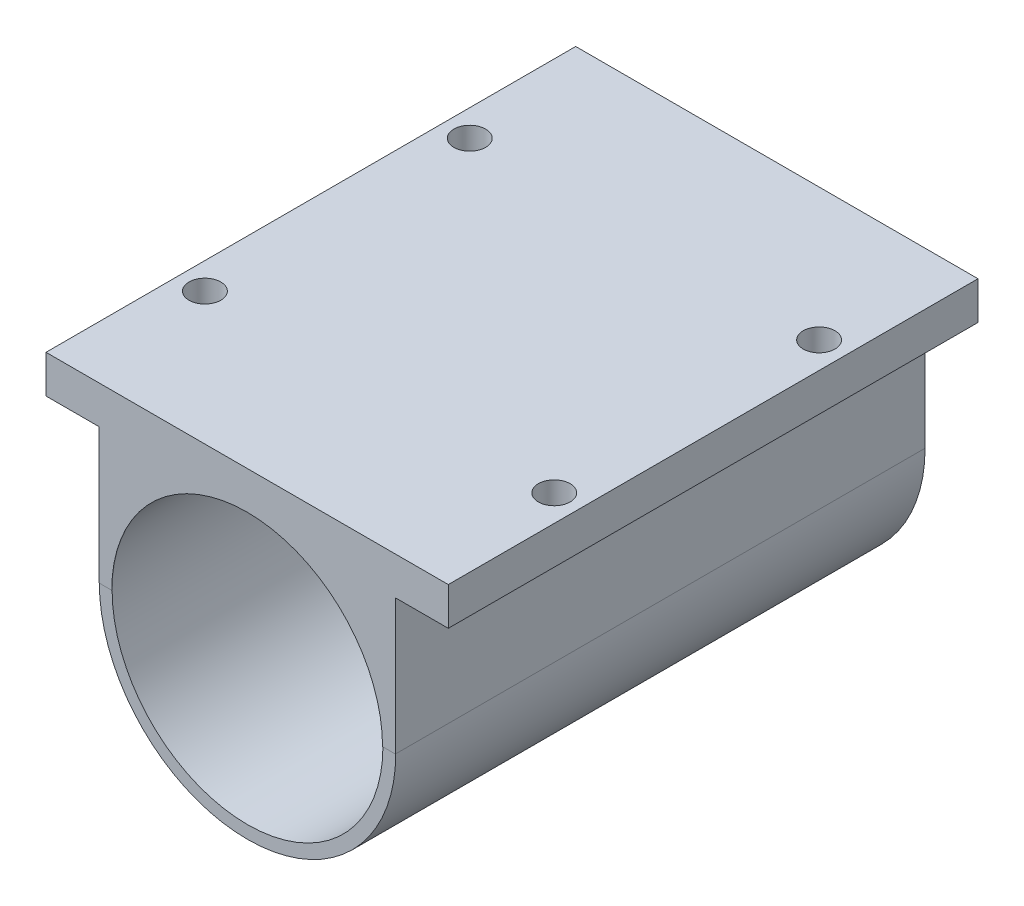
SolidWorks part; units mm, degrees
ref_plane "Front Plane" through (0, 0, 0) normal (0, 0, 1) x (1, 0, 0)
ref_plane "Top Plane" through (0, 0, 0) normal (0, 1, 0) x (1, 0, 0)
ref_plane "Right Plane" through (0, 0, 0) normal (1, 0, 0) x (0, 0, -1)
sketch "Sketch1" plane through (0, 0, 0) normal (0, 0, 1) x (1, 0, 0)
  circle A0 centre (0, 0) radius 14
  dimension "D1" = 28
extrude "Boss-Extrude1" add sketch "Sketch1" along normal blind 50
sketch "Sketch5" plane through (0, 0, 0) normal (0, 1, 0) x (1, 0, 0)
  line L0 (-14, 0) -> (14, 0)
  line L1 (-14, 0) -> (-14, -50.0349)
  line L2 (14, 0) -> (14, -50.0349)
  line L3 (-14, -50.0349) -> (14, -50.0349)
extrude "Boss-Extrude2" add sketch "Sketch5" along normal blind 21
sketch "Sketch2" plane through (0, 0, 50) normal (0, 0, 1) x (1, 0, 0)
  circle A0 centre (0, 0) radius 12.7918
  circle A1 centre (0, 0) radius 14 construction
  dimension "D1" = 1.2082
  dimension "D2" = 1.2082
extrude "Cut-Extrude1" cut sketch "Sketch2" against normal blind 48 contours A0
sketch "Sketch3" plane through (0, 0, 0) normal (0, 0, -1) x (-1, 0, 0)
  circle A0 centre (0, 0) radius 4
  dimension "D1" = 8
extrude "Cut-Extrude2" cut sketch "Sketch3" against normal blind 49
sketch "Sketch4" plane through (0, 0, 0) normal (0, 0, -1) x (-1, 0, 0)
  line L0 (-14, 0) -> (14, 0) construction
  line L1 (0, 14) -> (0, -14) construction
  line L2 (14, 0) -> (0, 14) construction
  line L3 (0, 14) -> (7, 7) construction
  line L4 (7, 7) -> (-9.8995, -9.8995) construction
  circle A0 centre (0, 0) radius 14 construction
  circle A1 centre (0, -8.5) radius 1.5
  circle A2 centre (0, 8.5) radius 1.5
  circle A3 centre (8.5, 0) radius 1.5
  circle A4 centre (-8.5, 0) radius 1.5
  dimension "D1" = 8.5
  dimension "D2" = 8.5
  dimension "D3" = 45
  dimension "D4" = 8.5
  dimension "D5" = 8.5
extrude "Cut-Extrude3" cut sketch "Sketch4" against normal blind 49
sketch "Sketch6" plane through (0, 0, 50.0349) normal (0, 0, 1) x (1, 0, 0)
  circle A1 centre (0, 0) radius 12.79
extrude "Cut-Extrude5" cut sketch "Sketch6" against normal blind 21
sketch "Sketch7" plane through (0, 0, 50.0349) normal (0, 0, 1) x (1, 0, 0)
  line L0 (-14, 21) -> (14, 21)
  line L1 (-14, 21) -> (-14, 16.3653)
  line L2 (14, 21) -> (14, 16.3653)
  line L3 (-14, 16.3653) -> (14, 16.3653)
extrude "Cut-Extrude6" cut sketch "Sketch7" against normal blind 53
sketch "Sketch8" plane through (14, 0, 0) normal (1, 0, 0) x (0, 0, -1)
  line L0 (-50.0349, 16.3653) -> (0, 16.3653)
  line L1 (-50.0349, 16.3653) -> (-50.0349, 12.7853)
  line L2 (0, 16.3653) -> (0, 12.7853)
  line L3 (-50.0349, 12.7853) -> (0, 12.7853)
  dimension "D1" = 3.58
extrude "Boss-Extrude3" add sketch "Sketch8" along normal blind 5
sketch "Sketch13" plane through (0, 12.7853, 0) normal (0, -1, 0) x (1, 0, 0)
  line L0 (16.5, 50.0349) -> (16.5, 0) construction
  line L1 (19, 50.0349) -> (14, 50.0349) construction
  line L2 (19, 0) -> (14, 0) construction
  line L3 (14, 25.0174) -> (19, 25.0174) construction
  line L4 (14, 50.0349) -> (14, 0) construction
  line L5 (19, 50.0349) -> (19, 0) construction
  line L6 (14, 25.0174) -> (19, 50.0349) construction
  line L7 (14, 25.0174) -> (19, 0) construction
  circle A0 centre (16.5, 37.5262) radius 1.5
  circle A1 centre (16.5, 12.5087) radius 1.5
  dimension "D1" = 5
extrude "Cut-Extrude7" cut sketch "Sketch13" against normal blind 5
sketch "Sketch14" plane through (-14, 0, 0) normal (-1, 0, 0) x (0, 0, 1)
  line L0 (0, 16.3653) -> (50.0349, 16.3653)
  line L1 (0, 16.3653) -> (0, 12.7853)
  line L2 (50.0349, 16.3653) -> (50.0349, 12.7853)
  line L3 (0, 12.7853) -> (50.0349, 12.7853)
  dimension "D1" = 3.58
extrude "Boss-Extrude4" add sketch "Sketch14" along normal blind 5
sketch "Sketch15" plane through (0, 12.7853, 0) normal (0, -1, 0) x (1, 0, 0)
  line L0 (-16.5, 0) -> (-16.5, 50.0349) construction
  line L1 (-19, 0) -> (-14, 0) construction
  line L2 (-19, 50.0349) -> (-14, 50.0349) construction
  line L3 (-19, 25.0174) -> (-14, 25.0174) construction
  line L4 (-19, 0) -> (-19, 50.0349) construction
  line L5 (-14, 0) -> (-14, 50.0349) construction
  line L6 (-14, 0) -> (-19, 25.0174) construction
  line L7 (-19, 25.0174) -> (-14, 50.0349) construction
  circle A0 centre (-16.5, 12.5087) radius 1.5
  circle A1 centre (-16.5, 37.5262) radius 1.5
extrude "Cut-Extrude8" cut sketch "Sketch15" against normal blind 5
fillet "Fillet1" radius 1 1 edges at (10, 0, 0)
fillet "Fillet2" radius 1 3 edges at (1.5, 8.5, 0) (-10, 0, 0) (-1.5, -8.5, 0)
